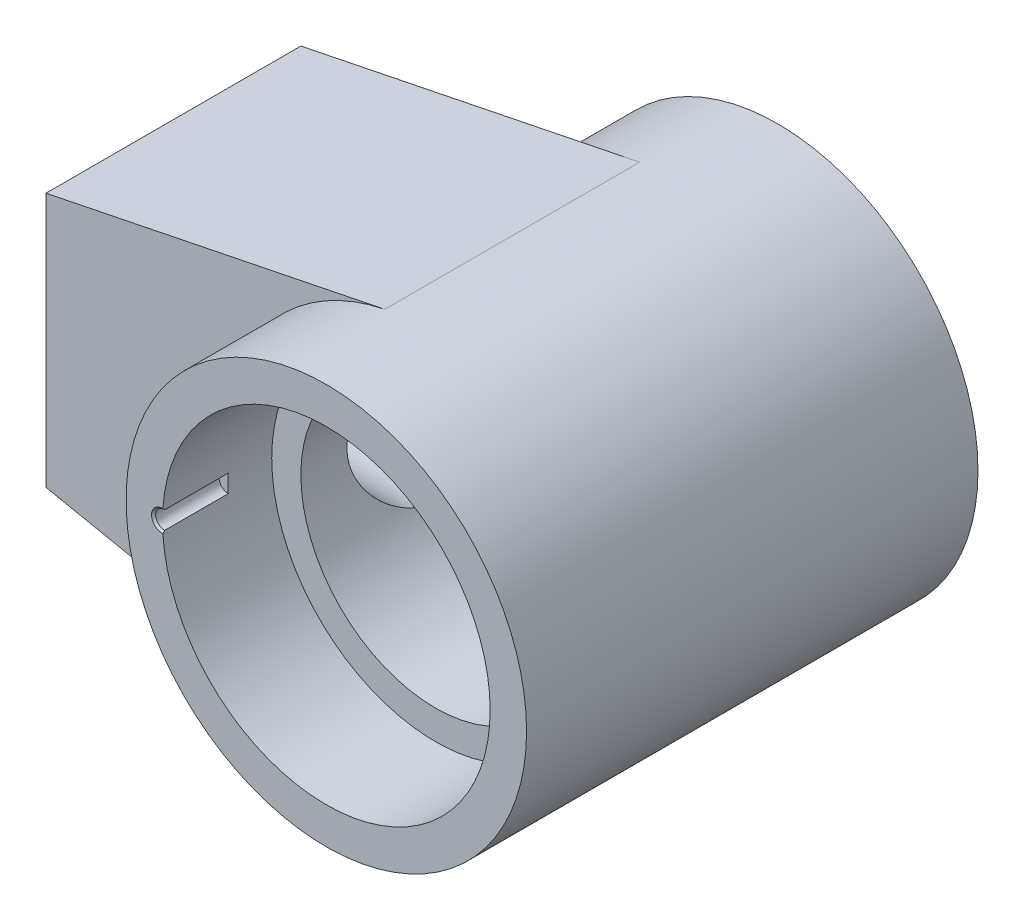
SolidWorks part; units mm, degrees
material "Сталь"
ref_plane "Спереди" through (0, 0, 0) normal (0, 0, 1) x (1, 0, 0)
ref_plane "Сверху" through (0, 0, 0) normal (0, 1, 0) x (1, 0, 0)
ref_plane "Справа" through (0, 0, 0) normal (1, 0, 0) x (0, 0, -1)
sketch "Эскиз1" plane through (0, 0, 0) normal (0, 0, 1) x (1, 0, 0)
  circle A0 centre (0, 0) radius 55
  dimension "D1" = 110
extrude "Бобышка-Вытянуть1" add sketch "Эскиз1" along normal mid plane 124
sketch "Эскиз2" plane through (0, 0, 0) normal (0, 0, 1) x (1, 0, 0)
  line L0 (0, 0) -> (-129.7535, 0) construction
  line L1 (-104, 0) -> (-104, 35)
  line L2 (-104, 35) -> (-10.9473, 53.8995)
  line L3 (-104, 0) -> (-10.9473, 0)
  line L4 (-10.9473, 0) -> (-10.9473, 53.8995)
  circle A0 centre (0, 0) radius 55 construction
  dimension "D1" = 70
  dimension "D2" = 104
extrude "Бобышка-Вытянуть2" add sketch "Эскиз2" along normal mid plane 70
mirror "Зеркальное отражение1" about plane through (-104, 0, 35) normal (0, 1, 0) of "Бобышка-Вытянуть2"
sketch "Эскиз3" plane through (0, 0, 0) normal (0, 0, 1) x (1, 0, 0)
  circle A0 centre (0, 0) radius 37
  dimension "D1" = 74
extrude "Вырез-Вытянуть1" cut sketch "Эскиз3" against normal through all and the other way through all contours A0
sketch "Эскиз4" plane through (0, 0, 62) normal (0, 0, 1) x (1, 0, 0)
  circle A0 centre (0, 0) radius 45
  dimension "D1" = 90
extrude "Вырез-Вытянуть2" cut sketch "Эскиз4" against normal blind 30
mirror "Зеркальное отражение2" about plane through (0, 0, 0) normal (0, 0, 1) of "Вырез-Вытянуть2"
sketch "Эскиз6" plane through (-104, 0, 0) normal (-1, 0, 0) x (0, 0, 1)
  circle A0 centre (0, 0) radius 19.352
  dimension "D1" = 38.704
extrude "Вырез-Вытянуть3" cut sketch "Эскиз6" against normal up to surface (67 mm away)
cosmetic thread "Условное изображение резьбы1" parameters "D2"=42
chamfer "Фаска2" distance 1.648 angle 45 1 edges at (-104, 0, 19.352)
sketch "Эскиз9" plane through (0, 0, -62) normal (0, 0, -1) x (-1, 0, 0)
  circle A0 centre (45, 0) radius 2.4455
  circle A1 centre (0, 0) radius 45 construction
  dimension "D1" = 4.891
extrude "Вырез-Вытянуть5" cut sketch "Эскиз9" against normal blind 18
cosmetic thread "Условное изображение резьбы2" parameters "D2"=6
mirror "Зеркальное отражение3" about plane through (0, 0, 0) normal (0, 0, 1) of "Вырез-Вытянуть5"
chamfer "Фаска3" distance 0.5545 angle 45 2 edges at (-47.4455, 0, -62) (-47.4455, 0, 62)
